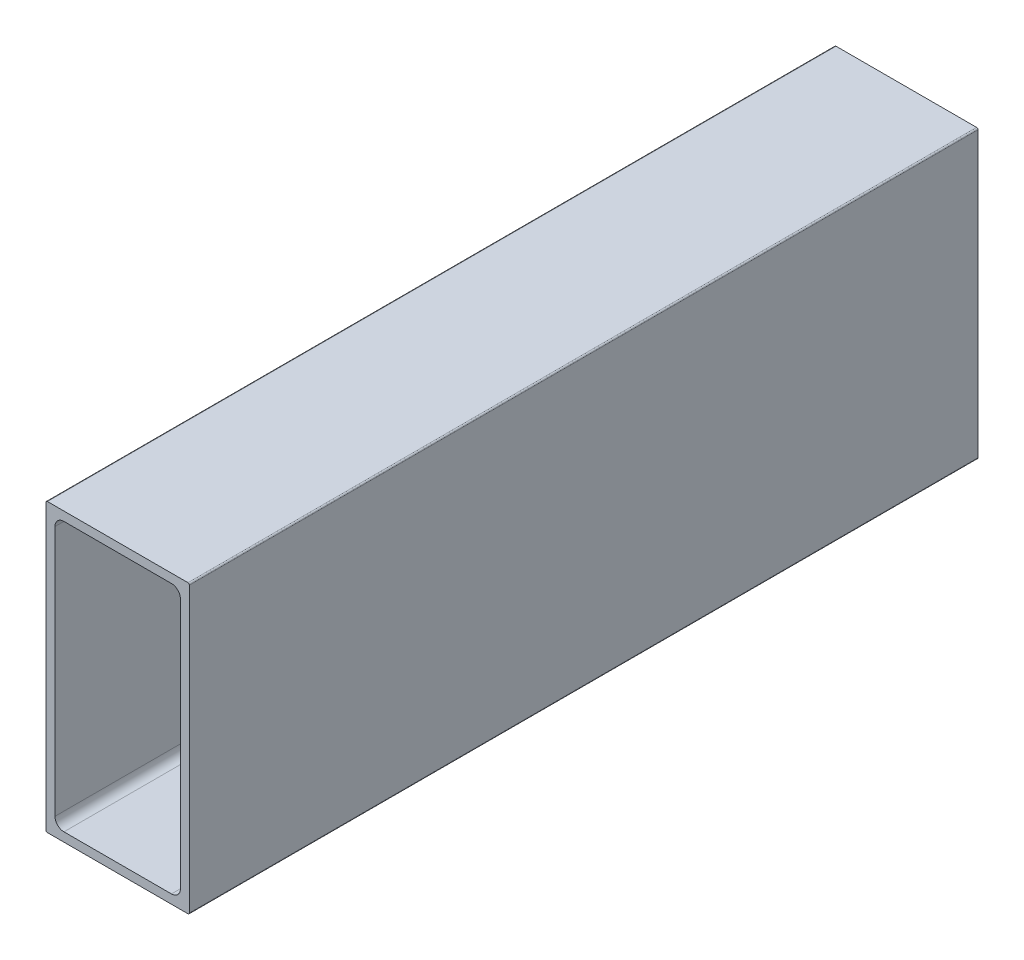
SolidWorks part; units mm, degrees
material "6061 Alloy"
ref_plane "Front Plane" through (0, 0, 0) normal (0, 0, 1) x (1, 0, 0)
ref_plane "Top Plane" through (0, 0, 0) normal (0, 1, 0) x (1, 0, 0)
ref_plane "Right Plane" through (0, 0, 0) normal (1, 0, 0) x (0, 0, -1)
ref_plane "Plane1" through (0, 0, 0) normal (0, 0, -1) x (-1, 0, 0)
sketch "Sketch1" plane through (0, 0, 0) normal (0, 0, -1) x (-1, 0, 0)
  line L0 (-11.1125, -22.225) -> (-11.1125, 22.225)
  line L1 (-9.525, 23.8125) -> (9.525, 23.8125)
  line L2 (11.1125, 22.225) -> (11.1125, -22.225)
  line L3 (9.525, -23.8125) -> (-9.525, -23.8125)
  line L4 (-12.7, 25.146) -> (-12.7, -25.146)
  line L5 (-12.446, -25.4) -> (12.446, -25.4)
  line L6 (12.7, -25.146) -> (12.7, 25.146)
  line L7 (12.446, 25.4) -> (-12.446, 25.4)
  arc A0 (-11.1125, 22.225) -> (-9.525, 23.8125) centre (-9.525, 22.225) cw
  arc A1 (9.525, 23.8125) -> (11.1125, 22.225) centre (9.525, 22.225) cw
  arc A2 (11.1125, -22.225) -> (9.525, -23.8125) centre (9.525, -22.225) cw
  arc A3 (-9.525, -23.8125) -> (-11.1125, -22.225) centre (-9.525, -22.225) cw
  arc A4 (-12.7, -25.146) -> (-12.446, -25.4) centre (-12.446, -25.146) ccw
  arc A5 (12.446, -25.4) -> (12.7, -25.146) centre (12.446, -25.146) ccw
  arc A6 (12.7, 25.146) -> (12.446, 25.4) centre (12.446, 25.146) ccw
  arc A7 (-12.446, 25.4) -> (-12.7, 25.146) centre (-12.446, 25.146) ccw
extrude "Boss-Extrude1" add sketch "Sketch1" against normal blind 139.7
